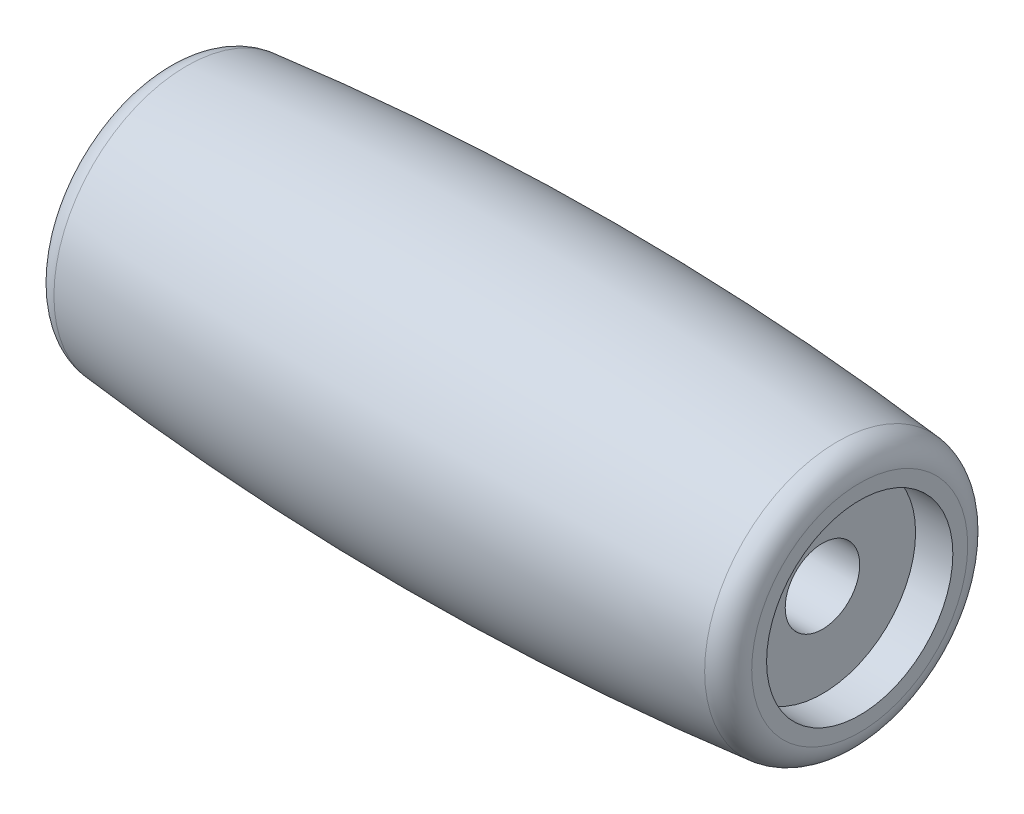
SolidWorks part; units mm, degrees
ref_plane "Front Plane" through (0, 0, 0) normal (0, 0, 1) x (1, 0, 0)
ref_plane "Top Plane" through (0, 0, 0) normal (0, 1, 0) x (1, 0, 0)
ref_plane "Right Plane" through (0, 0, 0) normal (1, 0, 0) x (0, 0, -1)
sketch "Sketch1" plane through (0, 0, 0) normal (0, 0, 1) x (1, 0, 0)
  line L0 (0, 0) -> (16.644, 0) construction
  line L1 (0, 0) -> (0, 6) construction
  line L2 (-12.5, 1.5) -> (12.5, 1.5)
  line L3 (12.5, 1.5) -> (12.5, 3.75)
  line L4 (12.5, 3.75) -> (14, 3.75)
  line L5 (14, 3.75) -> (14, 4.3486)
  line L6 (-14, 3.75) -> (-14, 4.3486)
  line L7 (-12.5, 3.75) -> (-14, 3.75)
  line L8 (-12.5, 1.5) -> (-12.5, 3.75)
  arc A0 (-13.1, 5.3436) -> (13.1, 5.3436) centre (0, -125.0417) cw
  arc A1 (14, 4.3486) -> (13.1, 5.3436) centre (13, 4.3486) ccw
  arc A2 (-14, 4.3486) -> (-13.1, 5.3436) centre (-13, 4.3486) cw
  point P13 (0, 1.5)
  point P14 (0, 6)
  point P17 (14, 5.25)
  point P20 (-14, 5.25)
  dimension "D7" = 1
  dimension "D1" = 14
  dimension "D2" = 1.5
  dimension "D3" = 1.5
  dimension "D4" = 3.75
  dimension "D5" = 1.5
  dimension "D6" = 6
revolve "Revolve1" add sketch "Sketch1" angle 360 about L0
scale "Scale1" scale about centroid uniform scaling yes scale factor 1.7
